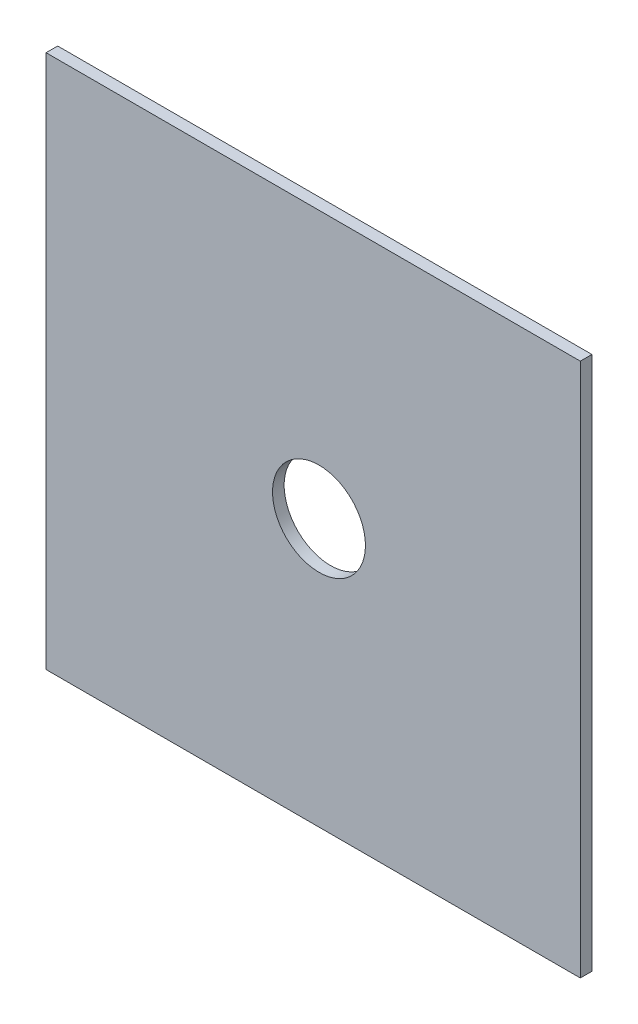
SolidWorks part; units mm, degrees
ref_plane "Front Plane" through (0, 0, 0) normal (0, 0, 1) x (1, 0, 0)
ref_plane "Top Plane" through (0, 0, 0) normal (0, 1, 0) x (1, 0, 0)
ref_plane "Right Plane" through (0, 0, 0) normal (1, 0, 0) x (0, 0, -1)
sketch "Sketch1" plane through (0, 0, 0) normal (0, 0, 1) x (1, 0, 0)
  line L1 (-74.6125, 142.875) -> (71.4375, 142.875)
  line L2 (-74.6125, 142.875) -> (-74.6125, -3.175)
  line L3 (-74.6125, -3.175) -> (71.4375, -3.175)
  line L4 (71.4375, 142.875) -> (71.4375, -3.175)
extrude "Boss-Extrude1" add sketch "Sketch1" along normal blind 3.175 contours L1 L4 L3 L2
sketch "Sketch2" plane through (0, 0, 3.175) normal (0, 0, 1) x (1, 0, 0)
  line L0 (-74.6125, 69.85) -> (0, 69.85)
  line L1 (-74.6125, 142.875) -> (-74.6125, -3.175) construction
  line L2 (0, 69.85) -> (0, -3.175)
  line L3 (-74.6125, -3.175) -> (71.4375, -3.175) construction
  circle A0 centre (0, 69.85) radius 12.7
  dimension "D1" = 25.4
extrude "Cut-Extrude1" cut sketch "Sketch2" against normal through all contours L0 A0 L2 | L2 A0 L0
